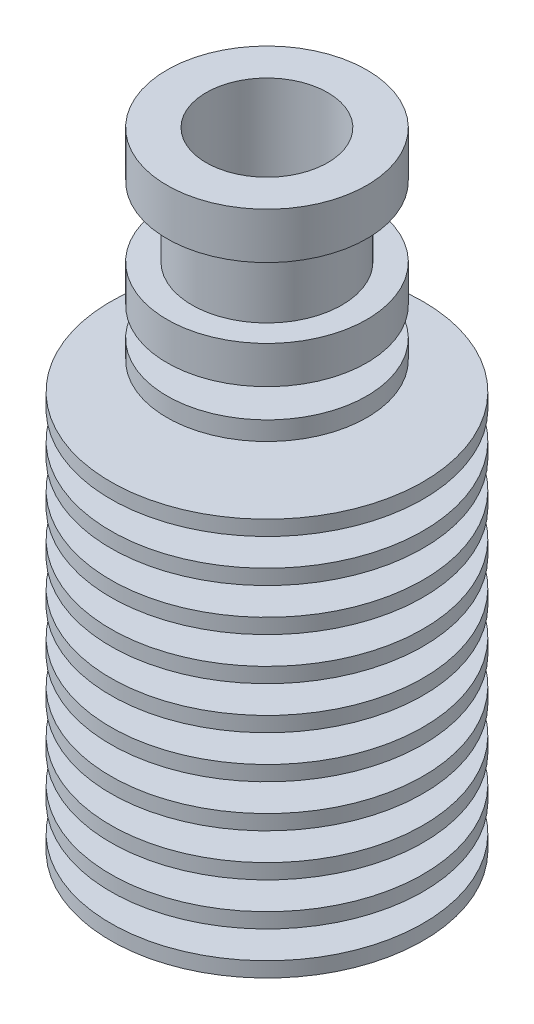
SolidWorks part; units mm, degrees
material "1060 Alloy"
ref_plane "Front Plane" through (0, 0, 0) normal (0, 0, 1) x (1, 0, 0)
ref_plane "Top Plane" through (0, 0, 0) normal (0, 1, 0) x (1, 0, 0)
ref_plane "Right Plane" through (0, 0, 0) normal (1, 0, 0) x (0, 0, -1)
sketch "Sketch1" plane through (0, 0, 0) normal (0, 0, 1) x (1, 0, 0)
  line L0 (0, -25.05) -> (0, 25.05) construction
  line L1 (3, -25.05) -> (12.5, -25.05)
  line L2 (12.5, -25.05) -> (12.5, -23.85)
  line L3 (12.5, -23.85) -> (7.5, -23.85)
  line L4 (7.5, -23.85) -> (7.5, -21.65)
  line L5 (7.5, -21.65) -> (12.5, -21.65)
  line L6 (12.5, -21.65) -> (12.5, -20.45)
  line L7 (12.5, -20.45) -> (7.5, -20.45)
  line L8 (7.5, -20.45) -> (7.5, -18.25)
  line L9 (7.5, -18.25) -> (12.5, -18.25)
  line L10 (12.5, -18.25) -> (12.5, -17.05)
  line L11 (12.5, -17.05) -> (7.5, -17.05)
  line L12 (7.5, -17.05) -> (7.5, -14.85)
  line L13 (7.5, -14.85) -> (12.5, -14.85)
  line L14 (12.5, -14.85) -> (12.5, -13.65)
  line L15 (12.5, -13.65) -> (7.5, -13.65)
  line L16 (7.5, -13.65) -> (7.5, -11.45)
  line L17 (7.5, -11.45) -> (12.5, -11.45)
  line L18 (12.5, -11.45) -> (12.5, -10.25)
  line L19 (12.5, -10.25) -> (7.5, -10.25)
  line L20 (7.5, -10.25) -> (7.5, -8.05)
  line L21 (7.5, -8.05) -> (12.5, -8.05)
  line L22 (12.5, -8.05) -> (12.5, -6.85)
  line L23 (12.5, -6.85) -> (6.5, -6.85)
  line L24 (6.5, -6.85) -> (6.5, -4.65)
  line L25 (6.5, -4.65) -> (12.5, -4.65)
  line L26 (12.5, -4.65) -> (12.5, -3.45)
  line L27 (12.5, -3.45) -> (4.5, -3.45)
  line L28 (4.5, -3.45) -> (4.5, -1.25)
  line L29 (4.5, -1.25) -> (12.5, -1.25)
  line L30 (12.5, -1.25) -> (12.5, -0.05)
  line L31 (12.5, -0.05) -> (4.5, -0.05)
  line L32 (4.5, -0.05) -> (4.5, 2.15)
  line L33 (4.5, 2.15) -> (12.5, 2.15)
  line L34 (12.5, 2.15) -> (12.5, 3.35)
  line L35 (12.5, 3.35) -> (4.5, 3.35)
  line L36 (4.5, 3.35) -> (4.5, 5.55)
  line L37 (4.5, 5.55) -> (12.5, 5.55)
  line L38 (12.5, 5.55) -> (12.5, 6.75)
  line L39 (12.5, 6.75) -> (4.5, 6.75)
  line L40 (4.5, 6.75) -> (4.5, 8.95)
  line L41 (4.5, 8.95) -> (8, 8.95)
  line L42 (8, 8.95) -> (8, 10.45)
  line L43 (8, 10.45) -> (4.5, 10.45)
  line L44 (4.5, 10.45) -> (4.5, 12.75)
  line L45 (4.5, 12.75) -> (8, 12.75)
  line L46 (8, 12.75) -> (8, 15.75)
  line L47 (8, 15.75) -> (6, 15.75)
  line L48 (6, 15.75) -> (6, 21.35)
  line L49 (6, 21.35) -> (8, 21.35)
  line L50 (8, 21.35) -> (8, 25.05)
  line L51 (3, -25.05) -> (3, -7.05)
  line L52 (3, -7.05) -> (1, -5.8953)
  line L53 (1, -5.8953) -> (1, 5.5119)
  line L54 (1, 5.5119) -> (2, 6.0892)
  line L55 (2, 6.0892) -> (2, 10.0892)
  line L56 (2, 10.0892) -> (4.8641, 15.05)
  line L57 (4.8641, 15.05) -> (4.8641, 25.05)
  line L58 (4.8641, 25.05) -> (8, 25.05)
  dimension "D1" = 50.1
  dimension "D2" = 3
  dimension "D3" = 25
  dimension "D4" = 1.2
  dimension "D5" = 2.2
  dimension "D6" = 15
  dimension "D7" = 13
  dimension "D8" = 9
  dimension "D9" = 9.3
  dimension "D10" = 3.7
  dimension "D11" = 16
  dimension "D12" = 12.3
  dimension "D13" = 14.6
  dimension "D14" = 12
  dimension "D15" = 2
  dimension "D16" = 4
  dimension "D17" = 18
  dimension "D18" = 4
  dimension "D19" = 10
  dimension "D20" = 150
  dimension "D21" = 4.8641
  dimension "D22" = 120
  dimension "D23" = 120
revolve "Revolve1" add sketch "Sketch1" angle 360 about L0
